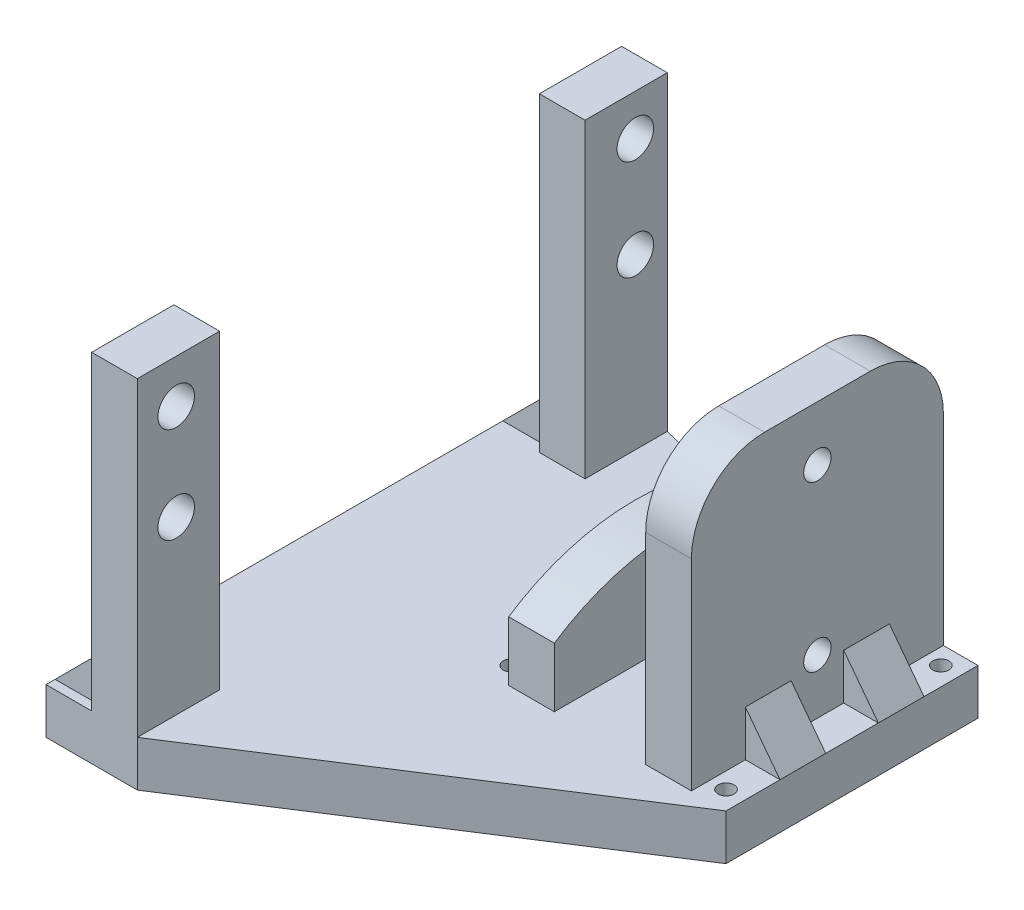
SolidWorks part; units mm, degrees
ref_plane "Front Plane" through (0, 0, 0) normal (0, 0, 1) x (1, 0, 0)
ref_plane "Top Plane" through (0, 0, 0) normal (0, 1, 0) x (1, 0, 0)
ref_plane "Right Plane" through (0, 0, 0) normal (1, 0, 0) x (0, 0, -1)
sketch "Sketch1" plane through (0, 0, 0) normal (0, 1, 0) x (1, 0, 0)
  line L0 (0, 13.7892) -> (27.5784, 13.7892) construction
  line L5 (0, 0) -> (27.5784, 0)
  line L6 (0, 0) -> (0, 27.5784)
  line L7 (0, 27.5784) -> (27.5784, 27.5784)
  line L8 (27.5784, 0) -> (27.5784, 27.5784)
  line L9 (13.7892, 0) -> (13.7892, 27.5784) construction
  line L10 (13.7892, 13.7892) -> (27.5784, 27.5784) construction
  line L11 (26.1642, 26.1642) -> (27.5784, 27.5784)
  line L12 (13.7892, 13.7892) -> (0, 27.5784) construction
  line L13 (1.4142, 26.1642) -> (0, 27.5784)
  line L14 (13.7892, 13.7892) -> (0, 0) construction
  line L15 (1.4142, 1.4142) -> (0, 0)
  line L16 (13.7892, 13.7892) -> (27.5784, 0) construction
  line L17 (26.1608, 1.4108) -> (27.5784, 0)
  circle A6 centre (2.0329, 2.0329) radius 0.875
  circle A8 centre (25.5455, 25.5455) radius 0.875
  circle A9 centre (2.0329, 25.5455) radius 0.875
  circle A10 centre (25.5455, 2.0329) radius 0.875
  dimension "D7" = 2
  dimension "D8" = 2
  dimension "D9" = 2
  dimension "D10" = 45
  dimension "D3" = 2
  dimension "D4" = 1.75
  dimension "D5" = 1.75
  dimension "D6" = 1.75
  dimension "D2" = 1.75
  dimension "D1" = 19.5009
  dimension "D11" = 45
  dimension "D12" = 45
extrude "Boss-Extrude1" add sketch "Sketch1" along normal blind 5
sketch "Sketch2" plane through (0, 5, 0) normal (0, 1, 0) x (1, 0, 0)
  line L0 (0, 13.7892) -> (27.5784, 13.7892) construction
  line L1 (0, 0) -> (0, 27.5784) construction
  line L2 (27.5784, 0) -> (27.5784, 27.5784) construction
  line L3 (13.7892, 27.5784) -> (13.7892, 0) construction
  line L4 (0, 27.5784) -> (27.5784, 27.5784) construction
  line L5 (0, 0) -> (27.5784, 0) construction
  line L7 (18.7892, 27.5784) -> (18.7892, 0)
  line L10 (8.7892, 0) -> (8.7892, 27.5784)
  line L12 (3.7892, 27.5784) -> (3.7892, 0)
  line L13 (3.7892, 0) -> (8.7892, 0)
  line L14 (3.7892, 27.5784) -> (8.7892, 27.5784)
  line L15 (18.7892, 27.5784) -> (23.7892, 27.5784)
  line L16 (23.7892, 27.5784) -> (23.7892, 0)
  line L17 (23.7892, 0) -> (18.7892, 0)
  dimension "D1" = 5
  dimension "D2" = 5
  dimension "D3" = 5
  dimension "D4" = 5
extrude "Boss-Extrude2" add sketch "Sketch2" along normal blind 30
sketch "Sketch3" plane through (23.7892, 0, 0) normal (1, 0, 0) x (0, 0, -1)
sketch "Sketch4" plane through (3.7892, 0, 0) normal (-1, 0, 0) x (0, 0, 1)
  line L0 (-13.7892, 35) -> (-13.7892, 0) construction
  line L1 (-27.5784, 35) -> (0, 35) construction
  line L2 (0, 0) -> (-27.5784, 0) construction
  line L3 (-27.5784, 11.5094) -> (-27.5784, 35)
  line L4 (-27.5784, 35) -> (-27.5784, 5) construction
  line L5 (-27.5784, 35) -> (0, 35)
  line L6 (0, 35) -> (0, 11.5094)
  line L7 (0, 35) -> (0, 5) construction
  arc A0 (0, 11.5094) -> (-27.5784, 11.5094) centre (-13.7892, -9.3439) ccw
  dimension "D1" = 50
extrude "Cut-Extrude2" cut sketch "Sketch4" against normal blind 10
sketch "Sketch5" plane through (23.7892, 0, 0) normal (1, 0, 0) x (0, 0, -1)
  line L0 (13.7892, 35) -> (13.7892, 5) construction
  line L1 (0, 35) -> (27.5784, 35) construction
  line L2 (0, 5) -> (27.5784, 5) construction
  line L3 (27.5784, 20) -> (0, 20) construction
  line L4 (27.5784, 35) -> (27.5784, 5) construction
  line L5 (0, 35) -> (0, 5) construction
  line L6 (13.7892, 27.5) -> (13.7892, 12.5)
  line L7 (13.7892, 20) -> (13.7892, 12.5) construction
  circle A0 centre (13.7892, 29) radius 1.5
  circle A1 centre (13.7892, 11) radius 1.5
  dimension "D1" = 3
  dimension "D2" = 3
  dimension "D3" = 15
  dimension "D4" = 7.5
extrude "Cut-Extrude3" cut sketch "Sketch5" against normal blind 24 contours A0 | A1
fillet "Fillet1" radius 8 1 edges at (21.2892, 35, 0)
fillet "Fillet2" radius 8 1 edges at (21.2892, 35, -27.5784)
sketch "Sketch6" plane through (0, 5, 0) normal (0, 1, 0) x (1, 0, 0)
  line L5 (0, 13.7892) -> (27.5784, 13.7892) construction
  line L6 (0, 0) -> (0, 27.5784) construction
  line L7 (27.5784, 0) -> (27.5784, 27.5784) construction
  line L8 (18.7892, 27.5784) -> (18.7892, 0) construction
  line L9 (8.7892, 27.5784) -> (18.7892, 27.5784)
  line L10 (8.7892, 27.5784) -> (8.7892, 17.5784)
  line L11 (8.7892, 17.5784) -> (18.7892, 17.5784)
  line L12 (18.7892, 27.5784) -> (18.7892, 17.5784)
  dimension "D2" = 10
extrude "Cut-Extrude5" cut sketch "Sketch6" against normal blind 7
sketch "Sketch7" plane through (0, 0, 0) normal (0, -1, 0) x (1, 0, 0)
  line L0 (0, -13.7892) -> (27.5784, -13.7892) construction
  line L1 (0, 0) -> (0, -27.5784) construction
  line L2 (27.5784, 0) -> (27.5784, -27.5784) construction
  line L3 (13.7892, 0) -> (13.7892, -17.5784) construction
  line L4 (0, 0) -> (27.5784, 0) construction
  line L5 (8.7892, -17.5784) -> (18.7892, -17.5784) construction
  circle A0 centre (13.7892, -13.7892) radius 3
  dimension "D1" = 6
extrude "Cut-Extrude6" cut sketch "Sketch7" against normal blind 7 contours A0
sketch "Sketch8" plane through (0, 5, 0) normal (0, 1, 0) x (1, 0, 0)
  line L0 (27.5784, 0) -> (27.5784, 27.5784) construction
  line L1 (27.5784, 21.6705) -> (23.7892, 21.6705)
  line L2 (27.5784, 21.6705) -> (27.5784, 22.5392)
  line L4 (23.7892, 21.6705) -> (23.7892, 22.5392)
  line L5 (23.7892, 0) -> (23.7892, 27.5784) construction
  line L6 (25.5455, 2.9079) -> (25.5455, 5.9079) construction
  line L7 (27.5784, 5.9079) -> (23.7892, 5.9079)
  line L8 (27.5784, 5.9079) -> (27.5784, 10.9079)
  line L9 (27.5784, 10.9079) -> (23.7892, 10.9079)
  line L10 (23.7892, 5.9079) -> (23.7892, 10.9079)
  line L11 (25.5455, 24.6705) -> (25.5455, 21.6705) construction
  line L12 (3.7892, 27.5784) -> (3.7892, 0) construction
  line L13 (23.7892, 21.6705) -> (27.5784, 21.6705)
  line L14 (23.7892, 21.6705) -> (23.7892, 16.6705)
  line L15 (23.7892, 16.6705) -> (27.5784, 16.6705)
  line L16 (27.5784, 21.6705) -> (27.5784, 16.6705)
  line L21 (0, 0) -> (0, 27.5784) construction
  line L22 (23.7892, 16.6705) -> (0, 16.6705) construction
  line L23 (3.7892, 10.9079) -> (0, 10.9079)
  line L24 (3.7892, 10.9079) -> (3.7892, 5.9079)
  line L25 (3.7892, 5.9079) -> (0, 5.9079)
  line L26 (0, 10.9079) -> (0, 5.9079)
  line L27 (23.7892, 21.6705) -> (0, 21.6705) construction
  line L28 (23.7892, 10.9079) -> (0, 10.9079) construction
  line L29 (23.7892, 5.9079) -> (0, 5.9079) construction
  line L30 (3.7892, 27.5784) -> (3.7892, 0) construction
  line L31 (0, 21.6705) -> (3.7892, 21.6705)
  line L32 (0, 21.6705) -> (0, 16.6705)
  line L33 (0, 16.6705) -> (3.7892, 16.6705)
  line L34 (3.7892, 21.6705) -> (3.7892, 16.6705)
  circle A0 centre (25.5455, 2.0329) radius 0.875 construction
  circle A1 centre (25.5455, 25.5455) radius 0.875 construction
  line M11 (23.7892, 27.5784) -> (23.7892, 0)
  line M13 (27.5784, 0) -> (27.5784, 27.5784)
  dimension "D1" = 3
  dimension "D2" = 3
  dimension "D3" = 5
  dimension "D4" = 5
extrude "Boss-Extrude3" add sketch "Sketch8" along normal blind 5 contours L34 L31 L32 L33 | L15 L1 M11 M13 | L9 L7 M13 M11 | L23 L26 L25 L24
sketch "Sketch9" plane through (0, 0, -5.9079) normal (0, 0, 1) x (1, 0, 0)
  line L0 (0, 5) -> (3.7892, 10)
  line L1 (3.7892, 10) -> (0, 10)
  line L2 (0, 10) -> (0, 5)
  line L3 (23.7892, 10) -> (27.5784, 5)
  line L4 (27.5784, 5) -> (27.5784, 10)
  line L5 (27.5784, 10) -> (23.7892, 10)
extrude "Cut-Extrude7" cut sketch "Sketch9" against normal blind 25 contours L2 L0 L1 | L5 L3 L4
sketch "Sketch10" plane through (0, 0, 0) normal (-1, 0, 0) x (0, 0, 1)
  line L1 (-27.5784, 5) -> (0, 5)
  line L2 (-27.5784, 5) -> (-27.5784, 0)
  line L3 (-27.5784, 0) -> (0, 0)
  line L4 (0, 5) -> (0, 0)
extrude "Boss-Extrude4" add sketch "Sketch10" along normal blind 11.61
sketch "Sketch11" plane through (-11.61, 0, 0) normal (-1, 0, 0) x (0, 0, 1)
  line L3 (-32.7584, 9.0171) -> (-32.7584, 0)
  line L4 (-32.7584, 0) -> (-27.5784, 0)
  line L6 (0, 0) -> (25.24, 0)
  line L8 (-32.7584, 9.0171) -> (-32.7584, 39)
  line L9 (-32.7584, 39) -> (-23.7584, 39)
  line L10 (-23.7584, 5) -> (-23.7584, 39)
  line L11 (25.24, 0) -> (25.24, 9.0171)
  line L12 (16.24, 5) -> (0, 5)
  line L14 (-27.5784, 0) -> (0, 0)
  line L16 (25.24, 9.0171) -> (25.24, 39)
  line L17 (25.24, 39) -> (16.24, 39)
  line L18 (16.24, 5) -> (16.24, 39)
  line L19 (0, 5) -> (-23.7584, 5)
  dimension "D1" = 39.9984
  dimension "D2" = 9
  dimension "D3" = 34
  dimension "D4" = 9
  dimension "D5" = 34
extrude "Boss-Extrude5" add sketch "Sketch11" along normal blind 5
sketch "Sketch17" plane through (-16.61, 0, 0) normal (-1, 0, 0) x (0, 0, 1)
  line L0 (-23.7584, 5) -> (-32.7584, 5)
  line L1 (-32.7584, 39) -> (-32.7584, 0) construction
  line L2 (-32.7584, 5) -> (-32.7584, 0)
  line L3 (-32.7584, 0) -> (25.24, 0)
  line L4 (25.24, 0) -> (25.24, 5)
  line L5 (25.24, 0) -> (25.24, 39) construction
  line L6 (25.24, 5) -> (-23.7584, 5)
extrude "Boss-Extrude9" add sketch "Sketch17" along normal blind 5
sketch "Sketch18" plane through (0, 5, 0) normal (0, 1, 0) x (1, 0, 0)
  line L0 (-16.61, 23.7584) -> (-16.61, 32.7584) construction
  line L1 (-16.61, 31.7584) -> (-21.61, 31.7584)
  line L2 (-16.61, 31.7584) -> (-16.61, 24.7584)
  line L3 (-16.61, 24.7584) -> (-21.61, 24.7584)
  line L4 (-21.61, 31.7584) -> (-21.61, 24.7584)
  line L5 (-21.61, -25.24) -> (-21.61, 32.7584) construction
  line L6 (-16.61, -25.24) -> (-16.61, -16.24) construction
  line L7 (-21.61, -17.24) -> (-16.61, -17.24)
  line L8 (-21.61, -17.24) -> (-21.61, -24.24)
  line L9 (-21.61, -24.24) -> (-16.61, -24.24)
  line L10 (-16.61, -17.24) -> (-16.61, -24.24)
  line L11 (-21.61, 32.7584) -> (-16.61, 32.7584) construction
  line L12 (-16.61, 23.7584) -> (-11.61, 23.7584) construction
  line L13 (-16.61, -16.24) -> (-11.61, -16.24) construction
  line L14 (-16.61, -25.24) -> (-11.61, -25.24) construction
  dimension "D1" = 1
  dimension "D2" = 1
  dimension "D3" = 1
  dimension "D4" = 1
extrude "Boss-Extrude10" add sketch "Sketch18" along normal blind 5
sketch "Sketch19" plane through (0, 0, 24.24) normal (0, 0, 1) x (1, 0, 0)
  line L0 (-21.61, 5) -> (-21.61, 10)
  line L1 (-21.61, 10) -> (-16.61, 10)
  line L2 (-16.61, 10) -> (-21.61, 5)
extrude "Cut-Extrude9" cut sketch "Sketch19" against normal blind 59
sketch "Sketch20" plane through (-11.61, 0, 0) normal (1, 0, 0) x (0, 0, -1)
  circle A0 centre (-20.9887, 34.2513) radius 2
  circle A1 centre (-20.9892, 23.7513) radius 2
  circle A2 centre (29.2608, 23.4989) radius 2
  circle A3 centre (29.2613, 34.4989) radius 2
extrude "Cut-Extrude10" cut sketch "Sketch20" against normal blind 10 contours A0 | A1 | A3 | A2
sketch "Sketch21" plane through (0, 5, 0) normal (0, 1, 0) x (1, 0, 0)
  line L0 (-11.61, -25.24) -> (27.5784, 0)
  line L1 (27.5784, 0) -> (-11.61, 0)
  line L2 (-11.61, 0) -> (-11.61, -25.24)
  line L3 (-11.61, 32.7584) -> (8.7892, 27.5784)
  line L4 (8.7892, 27.5784) -> (-11.61, 27.5784)
  line L5 (-11.61, 27.5784) -> (-11.61, 32.7584)
extrude "Boss-Extrude11" add sketch "Sketch21" against normal blind 5
